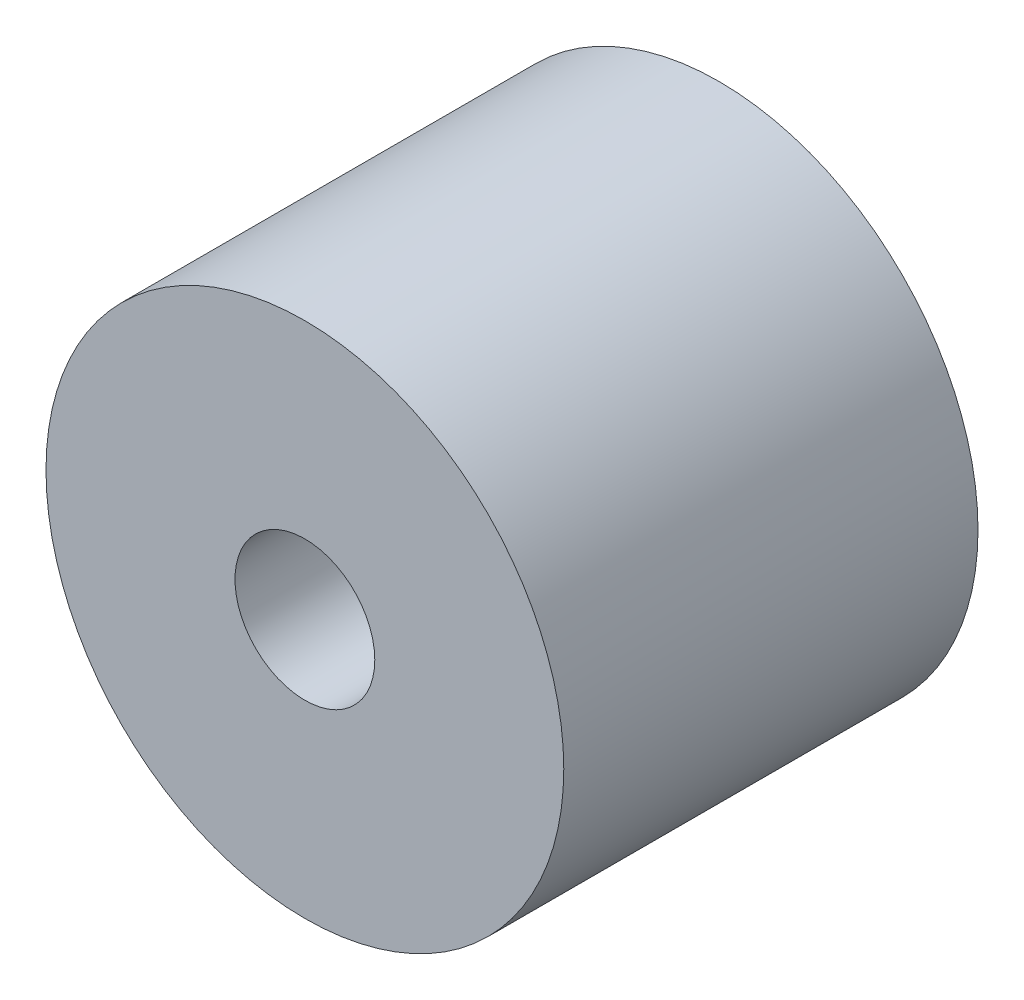
SolidWorks part; units mm, degrees
ref_plane "Front" through (0, 0, 0) normal (0, 0, 1) x (1, 0, 0)
ref_plane "Top" through (0, 0, 0) normal (0, 1, 0) x (1, 0, 0)
ref_plane "Right" through (0, 0, 0) normal (1, 0, 0) x (0, 0, -1)
sketch "Sketch1" plane through (0, 0, 0) normal (0, 0, 1) x (1, 0, 0)
  circle A0 centre (0, 0) radius 6.35
  circle A1 centre (0, 0) radius 1.7145
  dimension "D1" = 12.7
  dimension "D2" = 3.429
extrude "Boss-Extrude1" add sketch "Sketch1" against normal blind 10.16
